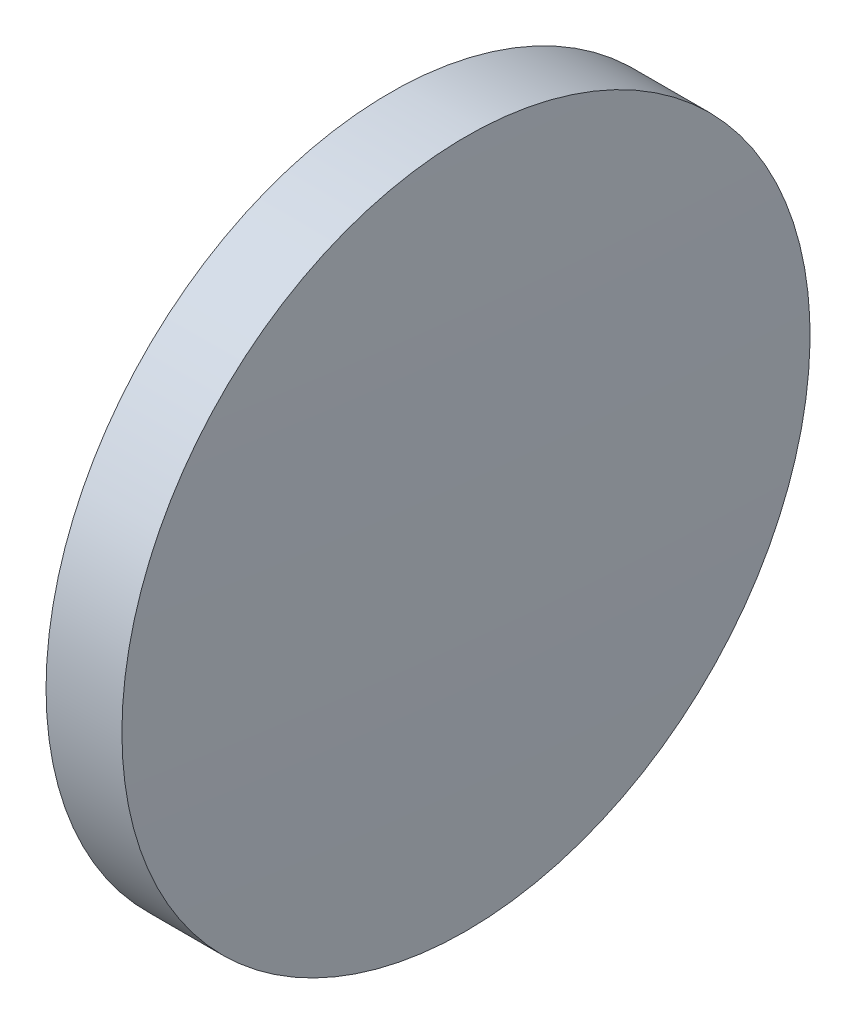
SolidWorks part; units mm, degrees
ref_plane "前视基准面" through (0, 0, 0) normal (0, 0, 1) x (1, 0, 0)
ref_plane "上视基准面" through (0, 0, 0) normal (0, 1, 0) x (1, 0, 0)
ref_plane "右视基准面" through (0, 0, 0) normal (1, 0, 0) x (0, 0, -1)
sketch "草图1" plane through (0, 0, 0) normal (0, 0, 1) x (1, 0, 0)
  line L0 (110.1654, 65.2336) -> (128.9614, 65.2336) construction
  line L1 (115.87, 65.2336) -> (115.87, 77.9336)
  line L2 (118.87, 65.2336) -> (115.87, 65.2336)
  line L5 (115.87, 77.9336) -> (118.67, 77.9336)
  arc A0 (118.87, 65.2336) -> (118.67, 77.9336) centre (-284.455, 65.2336) ccw
revolve "旋转1" add sketch "草图1" angle 360 about L0
